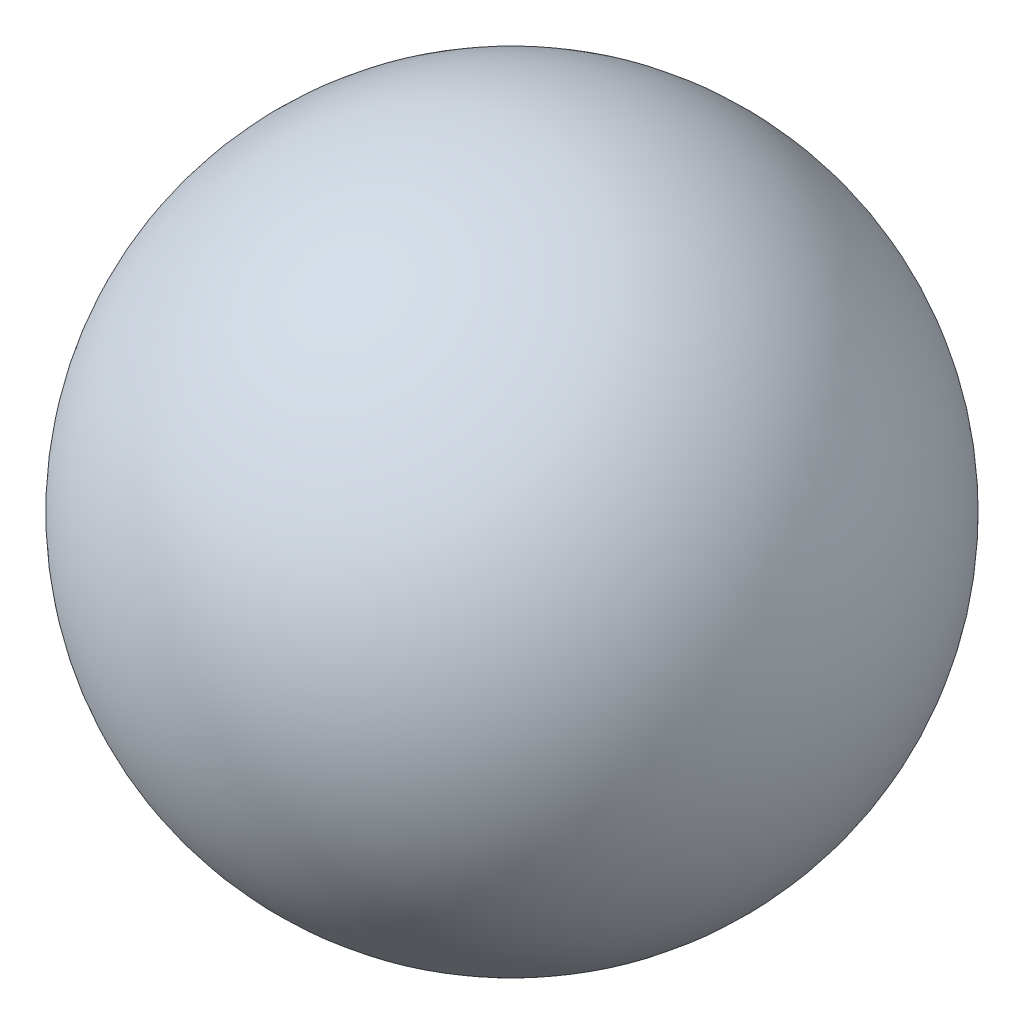
SolidWorks part; units mm, degrees
ref_plane "Спереди" through (0, 0, 0) normal (0, 0, 1) x (1, 0, 0)
ref_plane "Сверху" through (0, 0, 0) normal (0, 1, 0) x (1, 0, 0)
ref_plane "Справа" through (0, 0, 0) normal (1, 0, 0) x (0, 0, -1)
sketch "Sketch1" plane through (0, 0, 0) normal (0, 0, 1) x (1, 0, 0)
  line L0 (0, -300) -> (0, 300)
  arc A0 (0, -300) -> (0, 300) centre (0, 0) ccw
  dimension "D1" = 600
revolve "Revolve1" add sketch "Sketch1" angle 360 about L0
